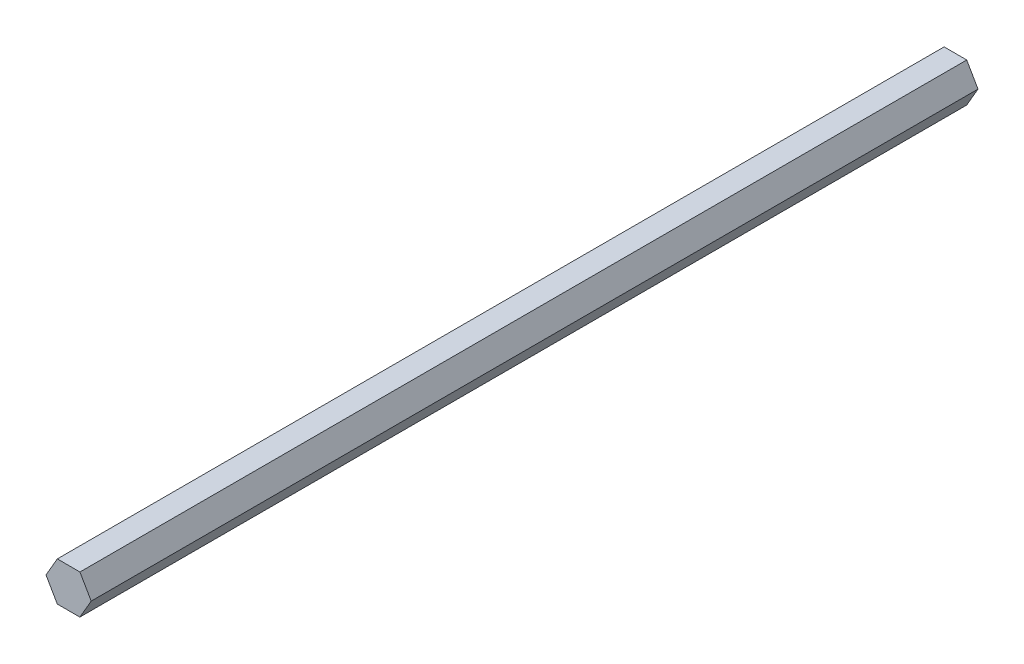
SolidWorks part; units mm, degrees
ref_plane "Front" through (0, 0, 0) normal (0, 0, 1) x (1, 0, 0)
ref_plane "Top" through (0, 0, 0) normal (0, 1, 0) x (1, 0, 0)
ref_plane "Right" through (0, 0, 0) normal (1, 0, 0) x (0, 0, -1)
sketch "Sketch1" plane through (0, 0, 0) normal (0, 0, 1) x (1, 0, 0)
  line L1 (0.7693, 1.3259) -> (-0.7636, 1.3292)
  line L2 (-0.7636, 1.3292) -> (-1.5329, 0.0033)
  line L3 (-1.5329, 0.0033) -> (-0.7693, -1.3259)
  line L4 (-0.7693, -1.3259) -> (0.7636, -1.3292)
  line L5 (0.7636, -1.3292) -> (1.5329, -0.0033)
  line L6 (1.5329, -0.0033) -> (0.7693, 1.3259)
  circle A0 centre (0, 0) radius 1.3275 construction
  dimension "D1" = 3.0658
extrude "Boss-Extrude1" add sketch "Sketch1" along normal blind 60.1599
sketch "Sketch2" plane through (0, 0, 0) normal (0, 0, -1) x (-1, 0, 0)
  circle A0 centre (0, 0) radius 1.4605
  dimension "D1" = 2.921
